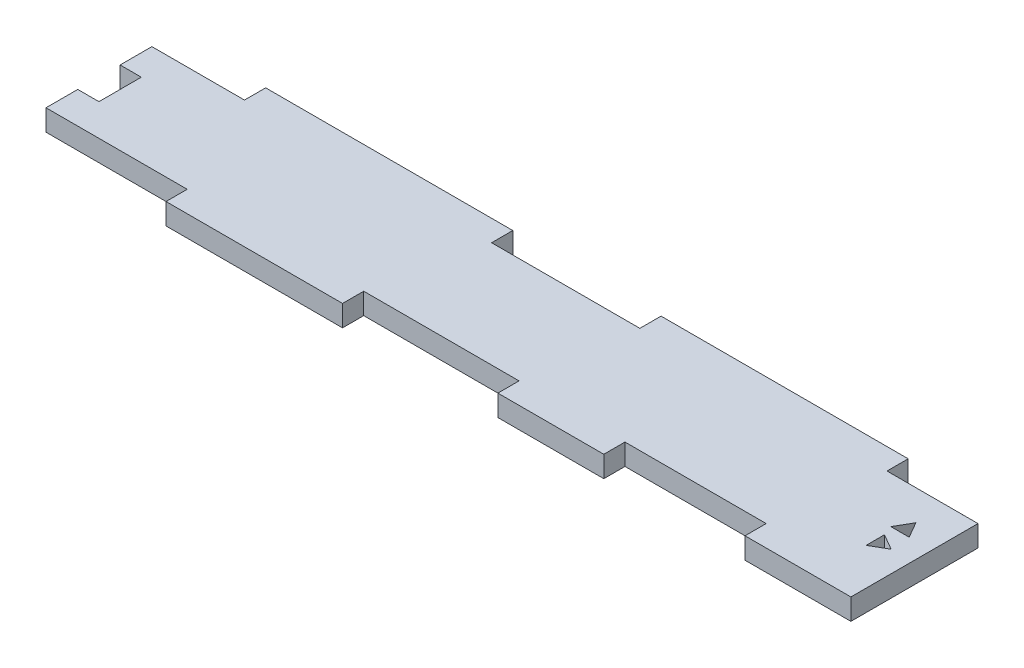
SolidWorks part; units mm, degrees
material "Acrylic (Medium-high impact)"
ref_plane "Plano frontal" through (0, 0, 0) normal (0, 0, 1) x (1, 0, 0)
ref_plane "Plano superior" through (0, 0, 0) normal (0, 1, 0) x (1, 0, 0)
ref_plane "Plano direito" through (0, 0, 0) normal (1, 0, 0) x (0, 0, -1)
sketch "Sketch1" plane through (0, 0, 0) normal (0, 1, 0) x (1, 0, 0)
  line L1 (-58.5, 7.5) -> (58.5, 7.5)
  line L2 (-58.5, 7.5) -> (-58.5, -7.5)
  line L3 (-58.5, -7.5) -> (58.5, -7.5)
  line L4 (58.5, 7.5) -> (58.5, -7.5)
  point P4 (0, 7.5)
  point P6 (-58.5, 0)
  dimension "D1" = 117
  dimension "D2" = 15
extrude "Boss-Extrude1" add sketch "Sketch1" along normal mid plane 3
sketch "Sketch2" plane through (0, 0, 0) normal (0, 1, 0) x (1, 0, 0)
  line L5 (-58.5, -7.5) -> (58.5, -7.5) construction
  line L6 (8.5, -7.5) -> (23.5, -7.5)
  line L7 (8.5, -7.5) -> (8.5, -10.5)
  line L8 (8.5, -10.5) -> (23.5, -10.5)
  line L9 (23.5, -7.5) -> (23.5, -10.5)
  line L11 (43.5, -7.5) -> (58.5, -7.5)
  line L12 (43.5, -7.5) -> (43.5, -10.5)
  line L13 (43.5, -10.5) -> (58.5, -10.5)
  line L14 (58.5, -7.5) -> (58.5, -10.5)
  line L15 (58.5, -7.5) -> (58.5, 7.5) construction
  dimension "D1" = 3
  dimension "D2" = 15
  dimension "D3" = 20
extrude "Boss-Extrude2" add sketch "Sketch2" along normal mid plane 3
sketch "Sketch12" plane through (0, 0, 0) normal (0, 1, 0) x (1, 0, 0)
  line L0 (-58.5, -7.5) -> (8.5, -7.5) construction
  line L1 (-38.5, -7.5) -> (-13.5, -7.5)
  line L2 (-38.5, -7.5) -> (-38.5, -10.5)
  line L3 (-38.5, -10.5) -> (-13.5, -10.5)
  line L4 (-13.5, -7.5) -> (-13.5, -10.5)
  line L5 (8.5, -10.5) -> (23.5, -10.5) construction
  line L6 (6.5, 7.5) -> (6.5, -7.5) construction
  line L7 (58.5, 7.5) -> (-58.5, 7.5) construction
  line L8 (-58.5, 7.5) -> (-58.5, -7.5) construction
  line L9 (6.5, 7.5) -> (-58.5, 7.5) construction
  line L10 (-26, 7.5) -> (-26, -7.5) construction
  point P18 (-26, -7.5)
  dimension "D2" = 25
  dimension "D3" = 20
  dimension "D4" = 20
extrude "Boss-Extrude3" add sketch "Sketch12" along normal mid plane 3
sketch "Sketch13" plane through (0, 0, 0) normal (0, 1, 0) x (1, 0, 0)
  line L0 (58.5, 7.5) -> (-58.5, 7.5) construction
  line L1 (-45.39, 7.5) -> (-10.39, 7.5)
  line L2 (-45.39, 7.5) -> (-45.39, 10.5)
  line L3 (-45.39, 10.5) -> (-10.39, 10.5)
  line L4 (-10.39, 7.5) -> (-10.39, 10.5)
  line L5 (58.5, -10.5) -> (58.5, 7.5) construction
  line L11 (-58.5, 7.5) -> (-58.5, -7.5) construction
  line L12 (10.61, 10.5) -> (45.61, 10.5)
  line L13 (10.61, 10.5) -> (10.61, 7.5)
  line L14 (10.61, 7.5) -> (45.61, 7.5)
  line L15 (45.61, 10.5) -> (45.61, 7.5)
  dimension "D1" = 3
  dimension "D2" = 35
  dimension "D3" = 13.11
  dimension "D4" = 21
  dimension "D5" = 12.89
extrude "Boss-Extrude4" add sketch "Sketch13" along normal mid plane 3
sketch "Sketch15" plane through (0, 0, 0) normal (0, 1, 0) x (1, 0, 0)
  line L0 (23.5, -7.5) -> (43.5, -7.5) construction
  line L4 (55.5, -1.799) -> (53.25, -0.5)
  line L5 (53.25, -0.5) -> (53.25, -3.0981)
  line L6 (54, 3.203) -> (52.701, 0.953)
  line L7 (53.25, -3.0981) -> (55.5, -1.799)
  line L8 (52.701, 0.953) -> (55.299, 0.953)
  line L9 (55.299, 0.953) -> (54, 3.203)
  line L10 (58.5, -10.5) -> (58.5, 7.5) construction
  line L11 (58.5, -10.5) -> (58.5, 7.5) construction
  circle A0 centre (54, -1.799) radius 1.5 construction
  circle A1 centre (54, 1.703) radius 1.5 construction
  dimension "D1" = 3
  dimension "D4" = 0.502
  dimension "D2" = 0.5
  dimension "D3" = 3
extrude "Cut-Extrude10" cut sketch "Sketch15" against normal through all both and the other way through all
sketch "Sketch16" plane through (0, 0, 0) normal (0, 1, 0) x (1, 0, 0)
  line L0 (-58.5, 7.5) -> (-58.5, -7.5) construction
  line L1 (-58.5, 3) -> (-55.5, 3)
  line L2 (-58.5, 3) -> (-58.5, -3)
  line L3 (-58.5, -3) -> (-55.5, -3)
  line L4 (-55.5, 3) -> (-55.5, -3)
  line L6 (-58.5, -7.5) -> (-38.5, -7.5) construction
  point P6 (-55.5, 0)
  dimension "D1" = 3
  dimension "D2" = 6
  dimension "D3" = 4.5
extrude "Cut-Extrude11" cut sketch "Sketch16" against normal through all both and the other way through all
equation "\"e\"=3.2892"
